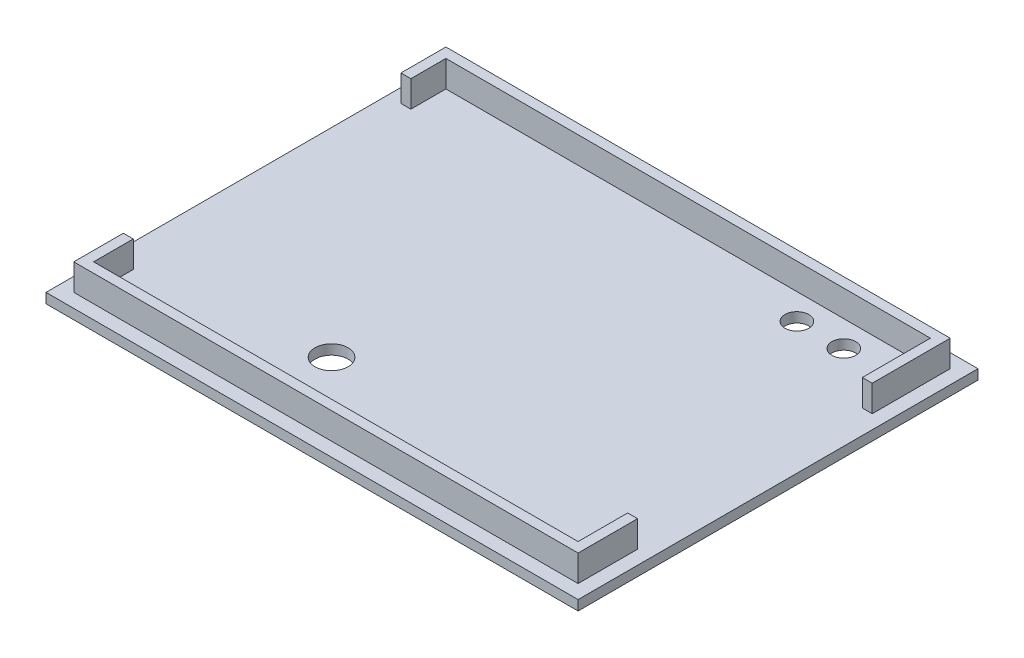
SolidWorks part; units mm, degrees
ref_plane "前视基准面" through (0, 0, 0) normal (0, 0, 1) x (1, 0, 0)
ref_plane "上视基准面" through (0, 0, 0) normal (0, 1, 0) x (1, 0, 0)
ref_plane "右视基准面" through (0, 0, 0) normal (1, 0, 0) x (0, 0, -1)
sketch "草图1" plane through (0, 0, 0) normal (0, 1, 0) x (1, 0, 0)
  line L0 (40.25, 30.25) -> (-40.25, 30.25)
  line L1 (38.15, -28.15) -> (-38.15, -28.15) construction
  line L2 (38.15, -28.15) -> (38.15, 28.15) construction
  line L3 (38.15, 28.15) -> (-38.15, 28.15) construction
  line L4 (-38.15, -28.15) -> (-38.15, 28.15) construction
  line L5 (38.15, -28.15) -> (-38.15, 28.15) construction
  line L6 (38.15, 28.15) -> (-38.15, -28.15) construction
  line L7 (-40.25, -30.25) -> (-40.25, 30.25)
  line L8 (40.25, -30.25) -> (-40.25, -30.25)
  line L9 (40.25, -30.25) -> (40.25, 30.25)
  line L10 (38.15, 28.15) -> (-38.15, 28.15) construction
  line L11 (-38.15, -28.15) -> (-38.15, 28.15) construction
  line L12 (38.15, -28.15) -> (-38.15, -28.15) construction
  line L13 (38.15, -28.15) -> (38.15, 28.15) construction
  point P0 (0, 0)
  dimension "D1" = 76.3
  dimension "D2" = 56.3
  dimension "D3" = 2.1
  dimension "D4" = 60.5
extrude "凸台-拉伸1" add sketch "草图1" along normal blind 1.5
sketch "草图2" plane through (0, 1.5, 0) normal (0, 1, 0) x (1, 0, 0)
  line L0 (38.15, -28.15) -> (-38.15, -28.15) construction
  line L1 (38.15, -28.15) -> (38.15, 28.15) construction
  line L2 (-38.15, -28.15) -> (-38.15, 28.15) construction
  line L3 (38.15, 28.15) -> (-38.15, 28.15) construction
  line L4 (38.15, 28.15) -> (-38.15, 28.15)
  line L5 (-38.15, -28.15) -> (-38.15, 28.15)
  line L6 (38.15, -28.15) -> (38.15, 28.15)
  line L7 (38.15, -28.15) -> (-38.15, -28.15)
  line L8 (36.65, 26.65) -> (-36.65, 26.65)
  line L9 (-36.65, -26.65) -> (-36.65, 26.65)
  line L10 (36.65, -26.65) -> (-36.65, -26.65)
  line L11 (36.65, -26.65) -> (36.65, 26.65)
  dimension "D1" = 1.5
extrude "凸台-拉伸2" add sketch "草图2" along normal blind 4
sketch "草图4" plane through (0, 5.5, 0) normal (0, 1, 0) x (1, 0, 0)
  line L1 (36.4, -19.15) -> (38.4, -19.15)
  line L2 (36.4, -19.15) -> (36.4, 16.35)
  line L3 (36.4, 16.35) -> (38.4, 16.35)
  line L4 (38.4, -19.15) -> (38.4, 16.35)
  line L5 (36.65, -26.65) -> (36.65, 26.65) construction
  line L6 (-38.15, -28.15) -> (38.15, -28.15) construction
  line L7 (-38.15, 28.15) -> (-38.15, -28.15) construction
  line L8 (-36.4, -20.65) -> (-38.4, -20.65)
  line L9 (-36.4, -20.65) -> (-36.4, 21.35)
  line L10 (-36.4, 21.35) -> (-38.4, 21.35)
  line L11 (-38.4, -20.65) -> (-38.4, 21.35)
  dimension "D1" = 35.5
  dimension "D2" = 2
  dimension "D3" = 0.25
  dimension "D4" = 9
  dimension "D5" = 42
  dimension "D6" = 2
  dimension "D7" = 0.25
  dimension "D8" = 7.5
extrude "切除-拉伸1" cut sketch "草图4" against normal blind 4
sketch "草图5" plane through (0, 0, 0) normal (0, -1, 0) x (1, 0, 0)
  line L0 (38.15, -28.15) -> (-38.15, -28.15) construction
  line L1 (38.15, 28.15) -> (38.15, -28.15) construction
  line L2 (38.15, 28.15) -> (-38.15, 28.15) construction
  line L3 (-38.15, 28.15) -> (-38.15, -28.15) construction
  circle A0 centre (20.35, -22.75) radius 1.8
  circle A1 centre (27.45, -22.75) radius 1.8
  circle A2 centre (-10.15, 17.15) radius 2.5
  dimension "D5" = 11
  dimension "D1" = 5.4
  dimension "D2" = 5.4
  dimension "D3" = 7.1
  dimension "D4" = 10.7
  dimension "D6" = 28
extrude "切除-拉伸2" cut sketch "草图5" against normal blind 3
